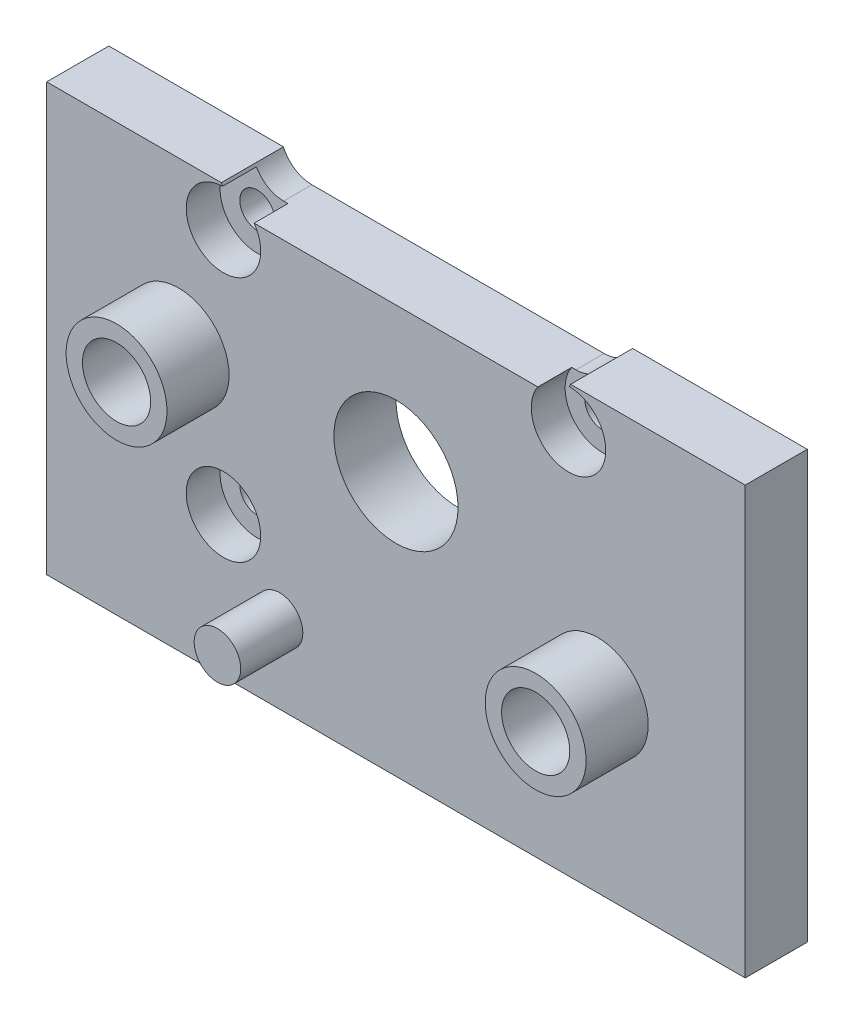
SolidWorks part; units mm, degrees
material "6061-T6 Al"
ref_plane "Front" through (0, 0, 0) normal (0, 0, 1) x (1, 0, 0)
ref_plane "Top" through (0, 0, 0) normal (0, 1, 0) x (1, 0, 0)
ref_plane "Right" through (0, 0, 0) normal (1, 0, 0) x (0, 0, -1)
ref_plane "Plane1" through (0, 0, 4) normal (0, 0, 1) x (1, 0, 0)
sketch "Sketch1" plane through (0, 0, 4) normal (0, 0, 1) x (1, 0, 0)
  line L0 (22.5, 10.5) -> (-22.5, 10.5)
  line L1 (-22.5, 10.5) -> (-22.5, -17)
  line L2 (-22.5, -17) -> (22.5, -17)
  line L3 (22.5, -17) -> (22.5, 10.5)
extrude "Boss-Extrude1" add sketch "Sketch1" against normal blind 4
sketch "Sketch2" plane through (0, 0, 0) normal (0, 0, -1) x (-1, 0, 0)
  line L0 (-9.417, 9.3) -> (9.417, 9.3)
  line L1 (11.25, 10.5) -> (-11.25, 10.5)
  arc A0 (-11.25, 10.5) -> (-9.417, 9.3) centre (-9.417, 11.3) ccw
  arc A1 (9.417, 9.3) -> (11.25, 10.5) centre (9.417, 11.3) ccw
extrude "Cut-Extrude1" cut sketch "Sketch2" against normal through all
ref_plane "Plane2" through (0, -6, 0) normal (0, 1, 0) x (1, 0, 0)
sketch "Sketch3" plane through (0, -6, 0) normal (0, 1, 0) x (1, 0, 0)
  line L0 (16.25, -4) -> (13, -4)
  line L1 (13, -4) -> (13, -8)
  line L2 (13, -8) -> (16.25, -8)
  line L3 (16.25, -8) -> (16.25, -4)
  line L4 (13, -4) -> (13, -8) construction
revolve "Revolve1" add sketch "Sketch3" angle 360 about L4
ref_plane "Plane3" through (0, -12, 0) normal (0, 1, 0) x (1, 0, 0)
sketch "Sketch4" plane through (0, -12, 0) normal (0, 1, 0) x (1, 0, 0)
  line L0 (-6, -4) -> (-7.5, -4)
  line L1 (-7.5, -4) -> (-7.5, -8)
  line L2 (-7.5, -8) -> (-6, -8)
  line L3 (-6, -8) -> (-6, -4)
  line L4 (-7.5, -4) -> (-7.5, -8) construction
revolve "Revolve2" add sketch "Sketch4" angle 360 about L4
sketch "Sketch5" plane through (0, 0, 0) normal (0, 1, 0) x (1, 0, 0)
  line L0 (-10.75, -4) -> (-14, -4)
  line L1 (-14, -4) -> (-14, -8)
  line L2 (-14, -8) -> (-10.75, -8)
  line L3 (-10.75, -8) -> (-10.75, -4)
  line L4 (-14, -4) -> (-14, -8) construction
revolve "Revolve3" add sketch "Sketch5" angle 360 about L4
hole_wizard "Ø8.0 (8) Diameter Hole1" positions "Sketch7" profile "Sketch6" hole size "Ø8.0" standard "ANSI Metric"
sketch "Sketch7" plane through (0, 0, 0) normal (0, 0, -1) x (-1, 0, 0)
  point P0 (0, 0)
sketch "Sketch6" plane through (0, 0, 0) normal (1, 0, 0) x (0, 1, 0)
  line L0 (0, 0) -> (0, 8)
  line L1 (0, 8) -> (4, 8)
  line L2 (4, 8) -> (4, 0)
  line L5 (4, 0) -> (0, 0)
  line L11 (0, -6.35) -> (0, 107.95) construction
  dimension "Thru Hole Dia." = 8
  dimension "Thru Hole Depth" = 8
hole_wizard "CBORE for M2 Hex Head Machine Screw1" positions "Sketch11" profile "Sketch10" counterbore size "M2" standard "ANSI Metric"
sketch "Sketch11" plane through (0, 0, 4) normal (0, 0, 1) x (1, 0, 0)
  point P0 (-11.113, -7.942)
  point P1 (-11.113, 7.938)
  point P2 (11.117, 7.938)
sketch "Sketch10" plane through (-11.113, -7.942, 4) normal (1, 0, 0) x (0, -1, 0)
  line L0 (0, 0) -> (0, 4)
  line L1 (0, 4) -> (1.13, 4)
  line L3 (1.13, 4) -> (1.13, 2.18)
  line L4 (1.13, 2.18) -> (2.4, 2.18)
  line L5 (2.4, 2.18) -> (2.4, 0)
  line L7 (2.4, 0) -> (0, 0)
  line L11 (0, -6.35) -> (0, 107.95) construction
  dimension "Thru Hole Dia." = 2.26
  dimension "Thru Hole Depth" = 4
  dimension "C'Bore Dia." = 4.8
  dimension "C'Bore Depth" = 2.18
hole_wizard "Tapped Hole for #8-32 Helicoil1" positions "Sketch13" profile "Sketch12" tap size "#8-32" standard "Helicoil® Inch"
sketch "Sketch13" plane through (0, 0, 8) normal (0, 0, 1) x (1, 0, 0)
  point P0 (-14, 0)
  point P3 (13, -6)
sketch "Sketch12" plane through (-14, 0, 8) normal (1, 0, 0) x (0, -1, 0)
  line L0 (0, 0) -> (0, 14.6552)
  line L1 (0, 14.6552) -> (2.1971, 13.335)
  line L2 (2.1971, 13.335) -> (2.1971, 0)
  line L5 (2.1971, 0) -> (0, 0)
  line L10 (0, 14.6552) -> (-2.1971, 13.335) construction
  line L11 (0, -6.35) -> (0, 107.95) construction
  dimension "Tap Drill Dia." = 4.3942
  dimension "Tap Drill Depth" = 13.335
  dimension "Drill Angle" = 118
